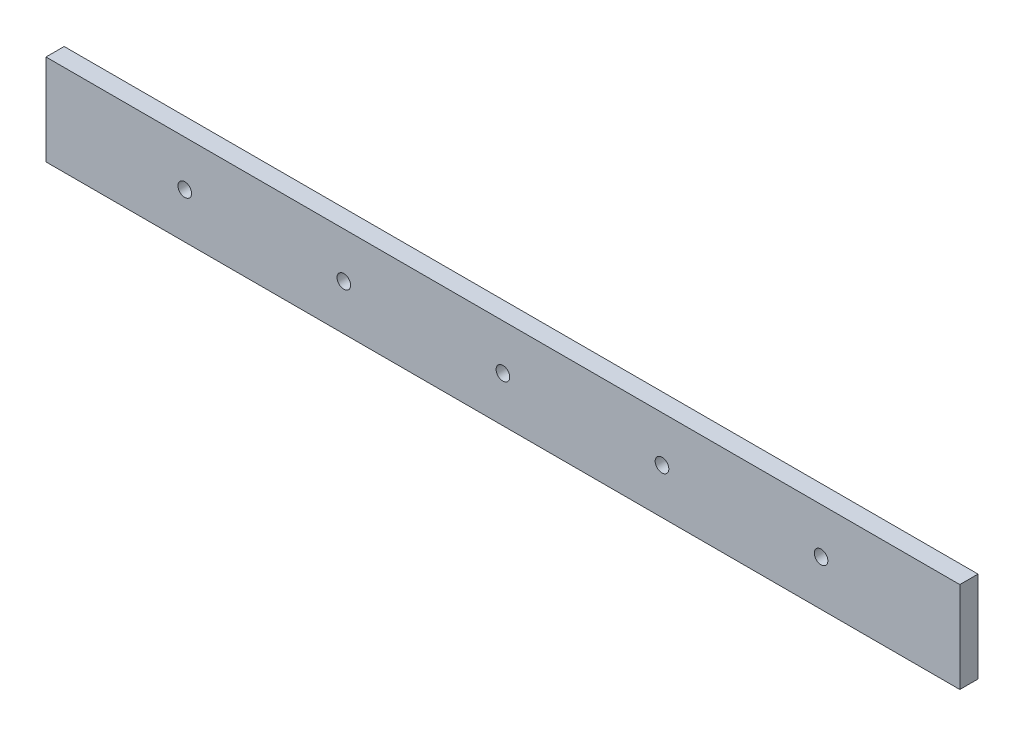
SolidWorks part; units mm, degrees
ref_plane "Front Plane" through (0, 0, 0) normal (0, 0, 1) x (1, 0, 0)
ref_plane "Top Plane" through (0, 0, 0) normal (0, 1, 0) x (1, 0, 0)
ref_plane "Right Plane" through (0, 0, 0) normal (1, 0, 0) x (0, 0, -1)
sketch "Sketch1" plane through (0, 0, 0) normal (0, 1, 0) x (1, 0, 0)
  line L1 (-100.53, 2) -> (100.53, 2)
  line L2 (-100.53, 2) -> (-100.53, -2)
  line L3 (-100.53, -2) -> (100.53, -2)
  line L4 (100.53, 2) -> (100.53, -2)
  line L5 (-100.53, 2) -> (100.53, -2) construction
  line L6 (-100.53, -2) -> (100.53, 2) construction
  point P0 (0, 0)
  dimension "D1" = 4
  dimension "D2" = 201.06
extrude "Boss-Extrude1" add sketch "Sketch1" along normal blind 20
sketch "Sketch2" plane through (0, 0, 2) normal (0, 0, 1) x (1, 0, 0)
  line L0 (-100.53, 10) -> (100.53, 10) construction
  line L1 (100.53, 20) -> (100.53, 0) construction
  line L2 (-100.53, 20) -> (-100.53, 0) construction
  circle A0 centre (-70, 10) radius 1.5
  circle A1 centre (-35, 10) radius 1.5
  circle A2 centre (0, 10) radius 1.5
  circle A3 centre (35, 10) radius 1.5
  circle A4 centre (70, 10) radius 1.5
  dimension "D1" = 3
  dimension "D2" = 30.53
  dimension "D4" = 30.53
  dimension "D3" = 5
extrude "Cut-Extrude1" cut sketch "Sketch2" against normal through all both and the other way through all
